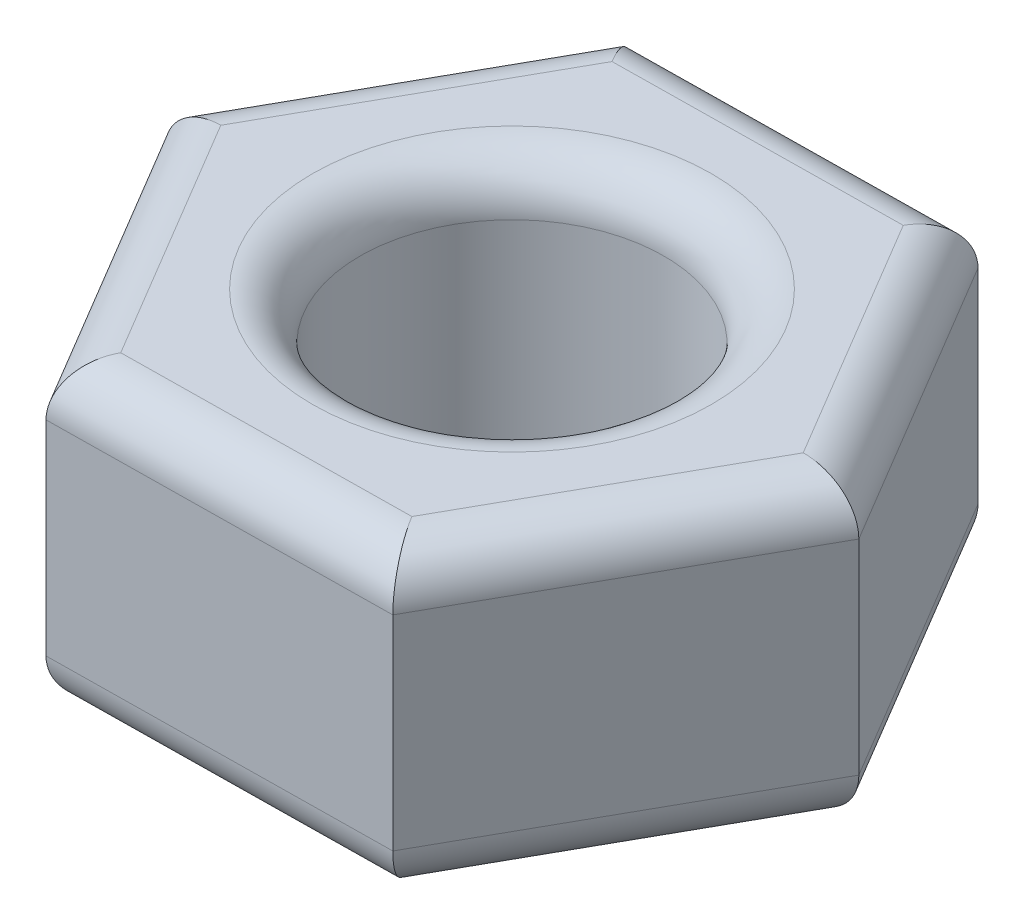
SolidWorks part; units mm, degrees
ref_plane "Спереди" through (0, 0, 0) normal (0, 0, 1) x (1, 0, 0)
ref_plane "Сверху" through (0, 0, 0) normal (0, 1, 0) x (1, 0, 0)
ref_plane "Справа" through (0, 0, 0) normal (1, 0, 0) x (0, 0, -1)
sketch "Sketch1" plane through (0, 0, 0) normal (0, 1, 0) x (1, 0, 0)
  line L1 (-3.6814, 6.1876) -> (-7.1994, -0.0944)
  line L2 (-7.1994, -0.0944) -> (-3.5179, -6.282)
  line L3 (-3.5179, -6.282) -> (3.6814, -6.1876)
  line L4 (3.6814, -6.1876) -> (7.1994, 0.0944)
  line L5 (7.1994, 0.0944) -> (3.5179, 6.282)
  line L6 (3.5179, 6.282) -> (-3.6814, 6.1876)
  circle A0 centre (0, 0) radius 7.2 construction
  circle A1 centre (0, 0) radius 3.2
  dimension "D1" = 14.4
  dimension "D2" = 6.4
extrude "Boss-Extrude1" add sketch "Sketch1" along normal blind 6.3
fillet "Fillet1" radius 1 14 edges at (0, 6.3, 3.2) (5.3587, 6.3, -3.1882) (5.4404, 6.3, 3.0466) (0.0817, 6.3, 6.2348) (-5.3587, 6.3, 3.1882) (-5.4404, 6.3, -3.0466) (-0.0817, 6.3, -6.2348) (0, 0, 3.2) (-5.4404, 0, -3.0466) (-5.3587, 0, 3.1882) (0.0817, 0, 6.2348) (5.4404, 0, 3.0466) (5.3587, 0, -3.1882) (-0.0817, 0, -6.2348)
